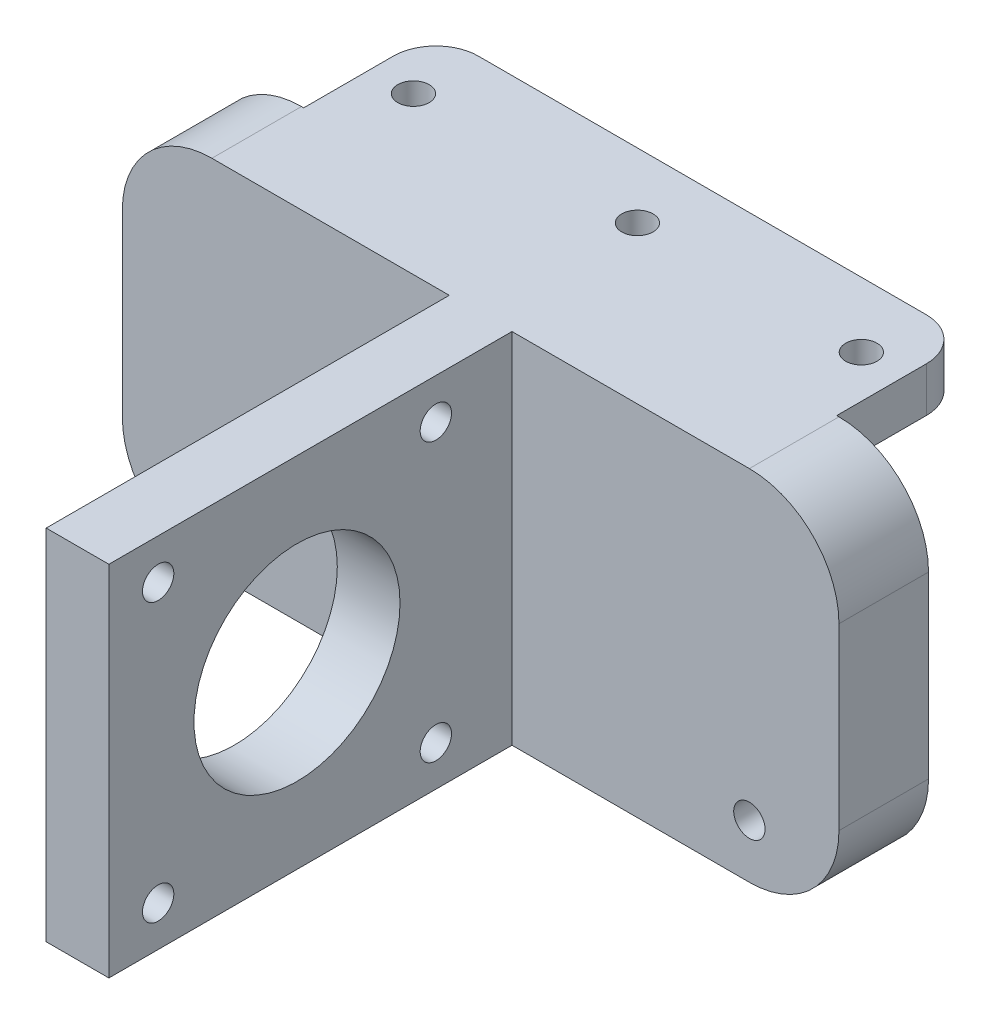
SolidWorks part; units mm, degrees
ref_plane "Front Plane" through (0, 0, 0) normal (0, 0, 1) x (1, 0, 0)
ref_plane "Top Plane" through (0, 0, 0) normal (0, 1, 0) x (1, 0, 0)
ref_plane "Right Plane" through (0, 0, 0) normal (1, 0, 0) x (0, 0, -1)
sketch "Sketch1" plane through (0, 0, 0) normal (0, 0, 1) x (1, 0, 0)
  line L0 (60, 35) -> (0, 35)
  line L1 (0, 35) -> (0, 40)
  line L2 (-10, 30) -> (-10, 10)
  line L3 (0, 0) -> (60, 0)
  line L4 (70, 10) -> (70, 30)
  line L5 (60, 40) -> (60, 35)
  arc A0 (0, 40) -> (-10, 30) centre (0, 30) ccw
  arc A1 (-10, 10) -> (0, 0) centre (0, 10) ccw
  arc A2 (60, 0) -> (70, 10) centre (60, 10) ccw
  arc A3 (70, 30) -> (60, 40) centre (60, 30) ccw
  point P14 (0, 0)
extrude "Boss-Extrude1" add sketch "Sketch1" along normal blind 10
sketch "Sketch2" plane through (0, 0, 10) normal (0, 0, 1) x (1, 0, 0)
  line L1 (0, 35) -> (60, 35)
  line L2 (0, 35) -> (0, 40)
  line L3 (0, 40) -> (60, 40)
  line L4 (60, 35) -> (60, 40)
extrude "Boss-Extrude2" add sketch "Sketch2" against normal blind 25
fillet "Fillet1" radius 5 2 edges at (60, 37.5, -15) (0, 37.5, -15)
sketch "Sketch3" plane through (0, 0, 10) normal (0, 0, 1) x (1, 0, 0)
  line L0 (0, 6) -> (0, 0) construction
  line L1 (60, 6) -> (60, 0) construction
  circle A0 centre (0, 6) radius 1.75
  circle A1 centre (60, 6) radius 1.75
  dimension "D1" = 3.5
  dimension "D2" = 6
extrude "Cut-Extrude1" cut sketch "Sketch3" against normal blind 25
sketch "Sketch4" plane through (0, 35, 0) normal (0, -1, 0) x (-1, 0, 0)
  line L0 (-55, 15) -> (-55, 7.5) construction
  line L1 (-30, 15) -> (-30, 7.5) construction
  line L2 (-5, 15) -> (-55, 15) construction
  line L3 (-5, 15) -> (-5, 7.5) construction
  arc A0 (0, 10) -> (-5, 15) centre (-5, 10) ccw construction
  circle A1 centre (-55, 7.5) radius 1.75
  circle A2 centre (-30, 7.5) radius 1.75
  circle A3 centre (-5, 7.5) radius 1.75
  dimension "D2" = 3.5
  dimension "D1" = 7.5
extrude "Cut-Extrude2" cut sketch "Sketch4" against normal blind 25
sketch "Sketch5" plane through (0, 35, 0) normal (0, -1, 0) x (1, 0, 0)
  line L0 (5, -14.75) -> (55, -14.75)
  line L1 (59.75, -10) -> (59.75, -0.25)
  line L3 (0.25, -0.25) -> (0.25, -10)
  line L4 (5, -15) -> (55, -15)
  line L5 (60, -10) -> (60, 0)
  line L6 (60, 0) -> (0, 0)
  line L7 (0, 0) -> (0, -10)
  line L8 (5, -15) -> (55, -15)
  line L9 (60, -10) -> (60, 0)
  line L10 (60, 0) -> (59.75, 0)
  line L11 (0, 0) -> (0, -10)
  line L12 (59.75, -0.25) -> (59.75, 0)
  line L13 (0.25, -0.25) -> (0.25, 0)
  line L14 (0.25, 0) -> (0, 0)
  line L16 (60, 0) -> (0, 0) construction
  line L17 (59.75, -0.25) -> (0.25, -0.25) construction
  arc A0 (55, -14.75) -> (59.75, -10) centre (55, -10) ccw
  arc A1 (0.25, -10) -> (5, -14.75) centre (5, -10) ccw
  arc A2 (55, -15) -> (60, -10) centre (55, -10) ccw
  arc A3 (0, -10) -> (5, -15) centre (5, -10) ccw
  arc A4 (55, -15) -> (60, -10) centre (55, -10) ccw
  arc A5 (0, -10) -> (5, -15) centre (5, -10) ccw
  dimension "D1" = 0
  dimension "D2" = 0.25
extrude "Cut-Extrude3" cut sketch "Sketch5" against normal blind 25
sketch "Sketch6" plane through (0, 0, 10) normal (0, 0, 1) x (1, 0, 0)
  line L0 (30, 40) -> (30, 0) construction
  line L1 (60, 40) -> (0, 40) construction
  line L2 (0, 0) -> (60, 0) construction
  line L4 (26.5, 40) -> (33.5, 40)
  line L5 (26.5, 40) -> (26.5, 0)
  line L6 (26.5, 0) -> (33.5, 0)
  line L7 (33.5, 40) -> (33.5, 0)
  line L8 (26.5, 40) -> (33.5, 0) construction
  line L9 (26.5, 0) -> (33.5, 40) construction
  point P6 (30, 20)
  dimension "D1" = 7
extrude "Boss-Extrude3" add sketch "Sketch6" along normal blind 45
sketch "Sketch7" plane through (33.5, 0, 0) normal (1, 0, 0) x (0, 0, -1)
  line L0 (-10, 20) -> (-58, 20) construction
  line L1 (-10, 0) -> (-10, 40) construction
  line L2 (-34, 20) -> (-49.5, 35.5) construction
  line L3 (-10, 40) -> (-10, 0) construction
  circle A0 centre (-34, 20) radius 11.5
  circle A1 centre (-49.5, 35.5) radius 1.75
  circle A2 centre (-18.5, 35.5) radius 1.75
  circle A3 centre (-18.5, 4.5) radius 1.75
  circle A4 centre (-49.5, 4.5) radius 1.75
  point P17 (-31, 20)
  point P18 (-32.5, 20)
  point P19 (-34.75, 16.25)
  point P22 (-34, 20)
  dimension "D2" = 23
  dimension "D4" = 3.5
  dimension "D1" = 24
  dimension "D3" = 15.5
  dimension "D5" = 15.5
  dimension "D6" = 4
extrude "Cut-Extrude4" cut sketch "Sketch7" against normal blind 45
